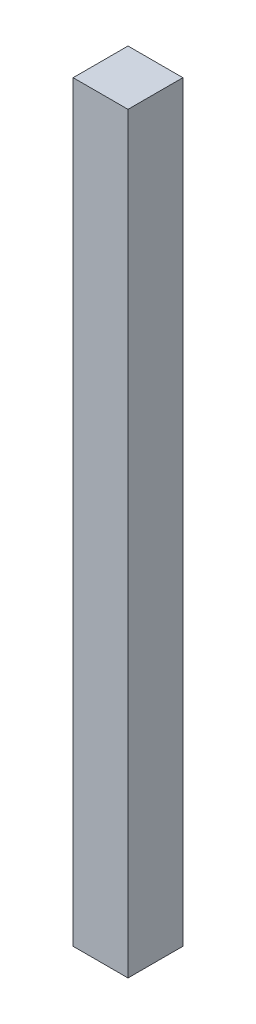
SolidWorks part; units mm, degrees
ref_plane "Front Plane" through (0, 0, 0) normal (0, 0, 1) x (1, 0, 0)
ref_plane "Top Plane" through (0, 0, 0) normal (0, 1, 0) x (1, 0, 0)
ref_plane "Right Plane" through (0, 0, 0) normal (1, 0, 0) x (0, 0, -1)
sketch "Sketch1" plane through (0, 0, 0) normal (0, 1, 0) x (1, 0, 0)
  line L0 (0, 0) -> (0, 88.9)
  line L1 (0, 88.9) -> (-88.9, 88.9)
  line L2 (-88.9, 88.9) -> (-88.9, 0)
  line L3 (-88.9, 0) -> (0, 0)
  dimension "D1" = 88.9
  dimension "D2" = 88.9
extrude "Boss-Extrude1" add sketch "Sketch1" along normal blind 1219.2 contours L1 L2 L3 L0
